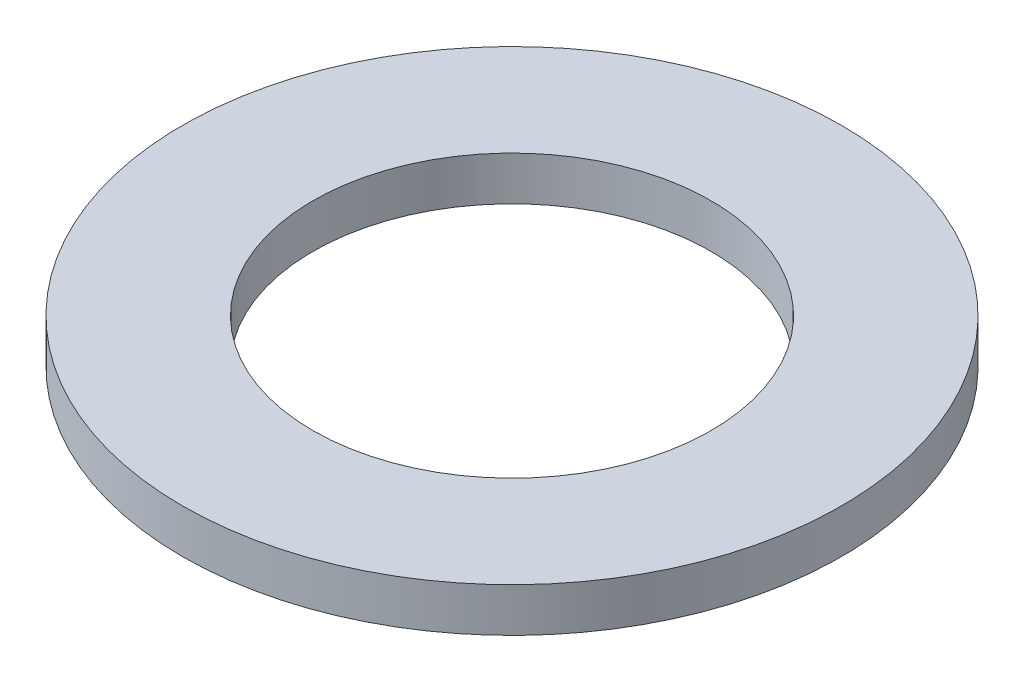
SolidWorks part; units mm, degrees
material "Brass"
ref_plane "Front Plane" through (0, 0, 0) normal (0, 0, 1) x (1, 0, 0)
ref_plane "Top Plane" through (0, 0, 0) normal (0, 1, 0) x (1, 0, 0)
ref_plane "Right Plane" through (0, 0, 0) normal (1, 0, 0) x (0, 0, -1)
sketch "Sketch1" plane through (0, 0, 0) normal (0, 1, 0) x (1, 0, 0)
  circle A0 centre (0, 0) radius 5.7547
  circle A1 centre (0, 0) radius 9.525
  dimension "D1" = 19.05
  dimension "D2" = 11.5094
extrude "Boss-Extrude1" add sketch "Sketch1" along normal blind 1.27
